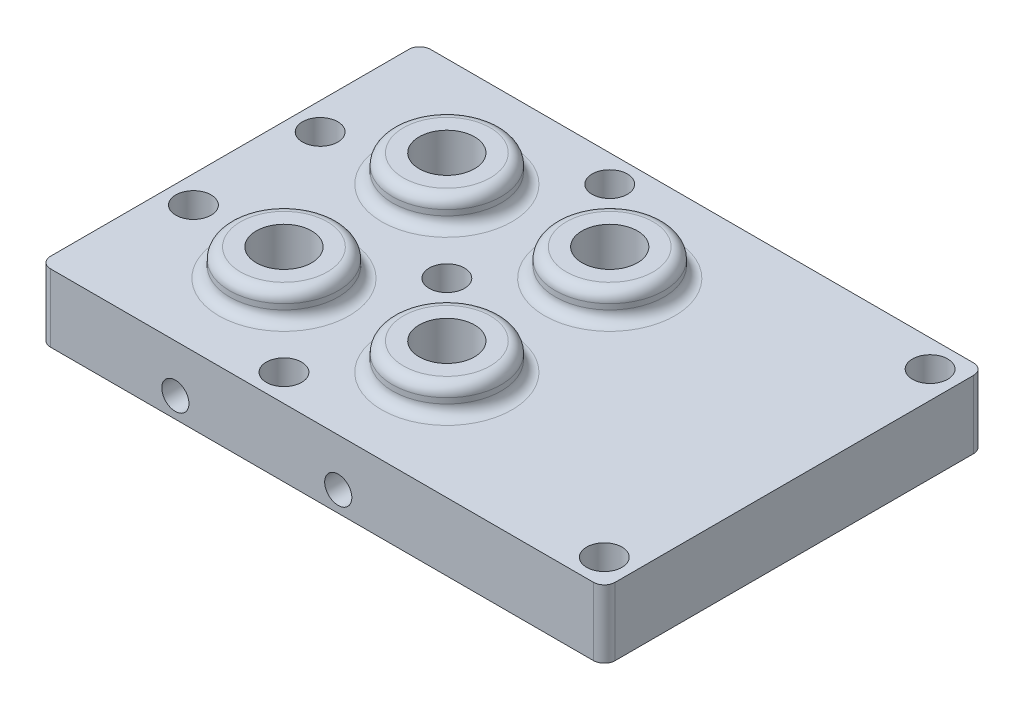
SolidWorks part; units mm, degrees
ref_plane "Front Plane" through (0, 0, 0) normal (0, 0, 1) x (1, 0, 0)
ref_plane "Top Plane" through (0, 0, 0) normal (0, 1, 0) x (1, 0, 0)
ref_plane "Right Plane" through (0, 0, 0) normal (1, 0, 0) x (0, 0, -1)
sketch "Sketch1" plane through (0, 0, 0) normal (0, 1, 0) x (1, 0, 0)
  line L1 (-50.5736, 28.472) -> (53.4264, 28.472)
  line L2 (-50.5736, 28.472) -> (-50.5736, -41.528)
  line L3 (-50.5736, -41.528) -> (53.4264, -41.528)
  line L4 (53.4264, 28.472) -> (53.4264, -41.528)
  dimension "D1" = 104
  dimension "D2" = 70
extrude "Boss-Extrude1" add sketch "Sketch1" along normal blind 5
sketch "Sketch4" plane through (0, 0, 0) normal (0, -1, 0) x (1, 0, 0)
  line L1 (-50.5736, 41.528) -> (53.4264, 41.528)
  line L2 (-50.5736, 41.528) -> (-50.5736, -28.472)
  line L3 (-50.5736, -28.472) -> (53.4264, -28.472)
  line L4 (53.4264, 41.528) -> (53.4264, -28.472)
  line L5 (-45.5736, 36.528) -> (48.4264, 36.528)
  line L6 (-45.5736, 36.528) -> (-45.5736, -23.472)
  line L7 (-45.5736, -23.472) -> (48.4264, -23.472)
  line L8 (48.4264, 36.528) -> (48.4264, -23.472)
  dimension "D1" = 5
  dimension "D2" = 5
  dimension "D3" = 5
  dimension "D4" = 5
extrude "Boss-Extrude3" add sketch "Sketch4" along normal blind 7.5
sketch "Sketch2" plane through (0, 5, 0) normal (0, 1, 0) x (-1, 0, 0)
  line L0 (50.5736, -28.472) -> (50.5736, 41.528) construction
  line L1 (-53.4264, -28.472) -> (50.5736, -28.472) construction
  line L2 (50.5736, 41.528) -> (-53.4264, 41.528) construction
  circle A0 centre (25.5736, -8.472) radius 10
  circle A1 centre (25.5736, 21.528) radius 10
  circle A2 centre (-4.4264, -8.472) radius 10
  circle A3 centre (-4.4264, 21.528) radius 10
  dimension "D1" = 20
  dimension "D4" = 20
  dimension "D2" = 25
  dimension "D3" = 20
  dimension "D5" = 20
extrude "Boss-Extrude2" add sketch "Sketch2" along normal blind 5 and the other way up to surface (12.5 mm away) other way up to face at (1.4264, -7.5, 6.528)
sketch "Sketch3" plane through (0, 10, 0) normal (0, 1, 0) x (1, 0, 0)
  circle A0 centre (-25.5736, 8.472) radius 5.1
  circle A1 centre (-25.5736, -21.528) radius 5.1
  circle A2 centre (4.4264, -21.528) radius 5.1
  circle A3 centre (4.4264, 8.472) radius 5.1
  dimension "D1" = 10.2
  dimension "D2" = 10.2
  dimension "D3" = 10.2
  dimension "D4" = 10.2
extrude "Cut-Extrude1" cut sketch "Sketch3" against normal through all
fillet "Fillet3" radius 2 8 edges at (4.4264, 10, 31.528) (-25.5736, 10, 31.528) (-25.5736, 5, 31.528) (4.4264, 5, 31.528) (4.4264, 5, 1.528) (4.4264, 10, 1.528) (-25.5736, 10, 1.528) (-25.5736, 5, 1.528)
sketch "Sketch5" plane through (0, 5, 0) normal (0, 1, 0) x (1, 0, 0)
  line L0 (53.4264, 28.472) -> (-50.5736, 28.472) construction
  line L1 (-50.5736, 28.472) -> (-50.5736, -41.528) construction
  line L2 (-50.5736, -41.528) -> (53.4264, -41.528) construction
  line L3 (53.4264, -41.528) -> (53.4264, 28.472) construction
  point P0 (48.4264, 23.472)
  point P1 (48.4264, -36.528)
  point P2 (-10.5736, -6.528)
  point P3 (-10.5736, -36.528)
  point P4 (-10.5736, 23.472)
  point P5 (-45.5736, 5.1387)
  point P6 (-45.5736, -18.1947)
  dimension "D1" = 23.3333
  dimension "D2" = 5
  dimension "D3" = 5
  dimension "D4" = 23.3333
  dimension "D5" = 35
  dimension "D6" = 40
  dimension "D7" = 5
  dimension "D8" = 5
  dimension "D9" = 5
  dimension "D10" = 5
sketch "Sketch8" plane through (0, 5, 0) normal (0, 1, 0) x (1, 0, 0)
  circle A0 centre (-10.5736, -36.528) radius 5
  circle A1 centre (-45.5736, -18.1947) radius 5
  circle A2 centre (-45.5736, 5.1387) radius 5
  circle A3 centre (-10.5736, -6.528) radius 5
  circle A4 centre (-10.5736, 23.472) radius 5
  circle A5 centre (48.4264, -36.528) radius 5
  circle A6 centre (48.4264, 23.472) radius 5
  dimension "D1" = 10
extrude "Boss-Extrude5" add sketch "Sketch8" against normal up to surface (12.5 mm away) up to face at (1.4264, -7.5, 6.528)
hole_wizard "CBORE for M3 SHCS2" positions "3DSketch2" profile "Sketch9" counterbore size "M3" standard "Ansi Metric" end condition through all
sketch3d "3DSketch2"
  point P0 (-45.5736, 5, -5.1387)
  point P3 (-10.5736, 5, -23.472)
  point P6 (-10.5736, 5, 6.528)
  point P9 (-45.5736, 5, 18.1947)
  point P12 (-10.5736, 5, 36.528)
  point P15 (48.4264, 5, 36.528)
  point P18 (48.4264, 5, -23.472)
sketch "Sketch9" plane through (-45.5736, 5, -5.1387) normal (1, 0, 0) x (0, 0, 1)
  line L0 (0, 0) -> (0, 12.5)
  line L1 (0, 12.5) -> (1.7, 12.5)
  line L3 (1.7, 12.5) -> (1.7, 8)
  line L4 (1.7, 8) -> (3.25, 8)
  line L5 (3.25, 8) -> (3.25, 0)
  line L7 (3.25, 0) -> (0, 0)
  line L11 (0, -6.35) -> (0, 107.95) construction
  dimension "Thru Hole Dia." = 3.4
  dimension "Thru Hole Depth" = 12.5
  dimension "C'Bore Dia." = 6.5
  dimension "C'Bore Depth" = 8
sketch "Sketch10" plane through (0, 0, 41.528) normal (0, 0, 1) x (1, 0, 0)
  line L0 (-50.5736, 5) -> (-50.5736, -7.5) construction
  line L2 (53.4264, -7.5) -> (-50.5736, -7.5) construction
  point P0 (-25.5736, -3.75)
  point P1 (4.4264, -3.75)
  dimension "D1" = 25
  dimension "D2" = 3.75
  dimension "D3" = 30
  dimension "D4" = 3.75
fillet "Fillet4" radius 2 4 edges at (53.4264, -1.25, 41.528) (53.4264, -1.25, -28.472) (-50.5736, -1.25, -28.472) (-50.5736, -1.25, 41.528)
hole_wizard "Tap Drill for M3x0.5 Tap3" positions "3DSketch4" profile "Sketch12" hole size "M3x0.5" standard "Ansi Metric"
sketch3d "3DSketch4"
  point P0 (-25.5736, -3.75, 41.528)
  point P3 (4.4264, -3.75, 41.528)
sketch "Sketch12" plane through (-25.5736, -3.75, 41.528) normal (1, 0, 0) x (0, -1, 0)
  line L0 (0, 0) -> (0, 20.7511)
  line L1 (0, 20.7511) -> (1.25, 20)
  line L2 (1.25, 20) -> (1.25, 0)
  line L5 (1.25, 0) -> (0, 0)
  line L10 (0, 20.7511) -> (-1.25, 20) construction
  line L11 (0, -6.35) -> (0, 107.95) construction
  dimension "Hole Dia." = 2.5
  dimension "Hole Depth" = 20
  dimension "Drill Angle" = 118
sketch "Sketch13" plane through (0, 0, 41.528) normal (0, 0, 1) x (1, 0, 0)
  circle A0 centre (-25.5736, -3.75) radius 2.5
  circle A1 centre (4.4264, -3.75) radius 2.5
  dimension "D1" = 5
  dimension "D2" = 5
extrude "Cut-Extrude2" cut sketch "Sketch13" against normal up to next
sketch "Sketch14" plane through (0, 0, -28.472) normal (0, 0, -1) x (-1, 0, 0)
  line L0 (48.5736, -7.5) -> (-51.4264, -7.5) construction
  line L1 (50.5736, 5) -> (50.5736, -7.5) construction
  point P0 (25.5736, -3.75)
  point P1 (-4.4264, -3.75)
  dimension "D1" = 3.75
  dimension "D2" = 3.75
  dimension "D3" = 25
  dimension "D4" = 30
hole_wizard "Tap Drill for M3x0.5 Tap4" positions "Sketch16" profile "Sketch15" hole size "M3x0.5" standard "Ansi Metric"
sketch "Sketch16" plane through (0, 0, -28.472) normal (0, 0, -1) x (-1, 0, 0)
  point P1 (25.5736, -3.75)
  point P6 (-4.4264, -3.75)
sketch "Sketch15" plane through (-25.5736, -3.75, -28.472) normal (1, 0, 0) x (0, 1, 0)
  line L0 (0, 0) -> (0, 20.7511)
  line L1 (0, 20.7511) -> (1.25, 20)
  line L2 (1.25, 20) -> (1.25, 0)
  line L5 (1.25, 0) -> (0, 0)
  line L10 (0, 20.7511) -> (-1.25, 20) construction
  line L11 (0, -6.35) -> (0, 107.95) construction
  dimension "Hole Dia." = 2.5
  dimension "Hole Depth" = 20
  dimension "Drill Angle" = 118
sketch "Sketch18" plane through (0, 0, -28.472) normal (0, 0, -1) x (-1, 0, 0)
  circle A0 centre (-4.4264, -3.75) radius 2.5
  circle A1 centre (25.5736, -3.75) radius 2.5
  dimension "D1" = 5
  dimension "D2" = 5
extrude "Cut-Extrude3" cut sketch "Sketch18" against normal up to next
